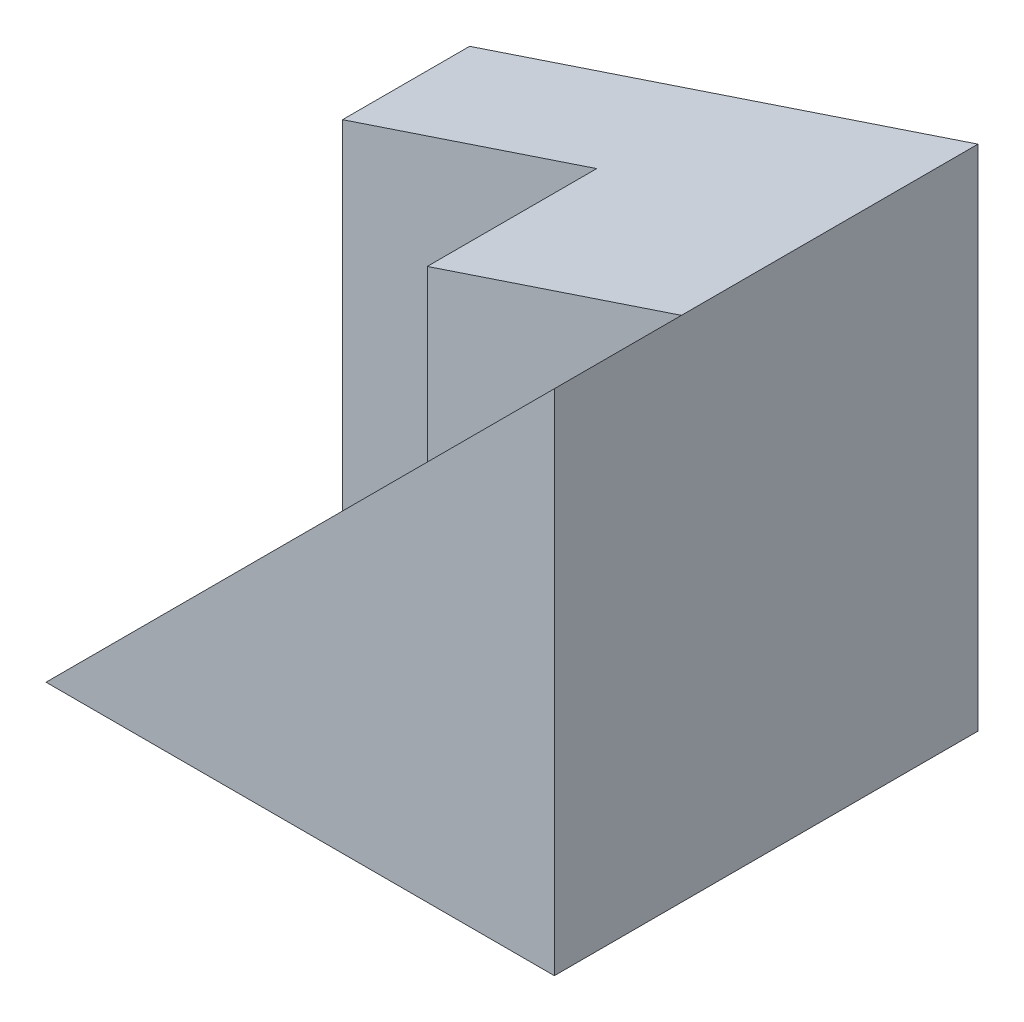
SolidWorks part; units mm, degrees
ref_plane "Front Plane" through (0, 0, 0) normal (0, 0, 1) x (1, 0, 0)
ref_plane "Top Plane" through (0, 0, 0) normal (0, 1, 0) x (1, 0, 0)
ref_plane "Right Plane" through (0, 0, 0) normal (1, 0, 0) x (0, 0, -1)
sketch "Sketch1" plane through (0, 0, 0) normal (0, 1, 0) x (1, 0, 0)
  line L1 (-3, -2.5) -> (3, -2.5)
  line L2 (-3, -2.5) -> (-3, 2.5)
  line L3 (-3, 2.5) -> (3, 2.5)
  line L4 (3, -2.5) -> (3, 2.5)
  line L5 (-3, -2.5) -> (3, 2.5) construction
  line L6 (-3, 2.5) -> (3, -2.5) construction
  point P0 (0, 0)
  dimension "D1" = 5
  dimension "D2" = 6
extrude "Boss-Extrude1" add sketch "Sketch1" along normal blind 6
sketch "Sketch2" plane through (0, 0, 2.5) normal (0, 0, 1) x (1, 0, 0)
  line L0 (3, 6) -> (-3, 0)
  line L1 (-3, 0) -> (-3, 6)
  line L2 (-3, 6) -> (3, 6)
extrude "Cut-Extrude1" cut sketch "Sketch2" against normal blind 3.5
sketch "Sketch3" plane through (0, 6, 0) normal (0, 1, 0) x (1, 0, 0)
  line L0 (3, 1) -> (-3, 1) construction
  line L1 (0, 1) -> (3, 1)
  line L2 (0, 1) -> (0, -1)
  line L3 (0, -1) -> (3, -1)
  line L4 (3, 1) -> (3, -1)
  line L5 (3, -2.5) -> (3, 1) construction
  dimension "D1" = 2
  dimension "D2" = 3
extrude "Boss-Extrude2" add sketch "Sketch3" against normal blind 3
sketch "Sketch4" plane through (0, 0, 1) normal (0, 0, 1) x (1, 0, 0)
  line L0 (3, 6) -> (-3, 4)
  line L1 (-3, 6) -> (-3, 0) construction
  line L2 (-3, 4) -> (-3, 6)
  line L3 (-3, 6) -> (3, 6)
  dimension "D1" = 2
extrude "Cut-Extrude2" cut sketch "Sketch4" against normal blind 3.5
